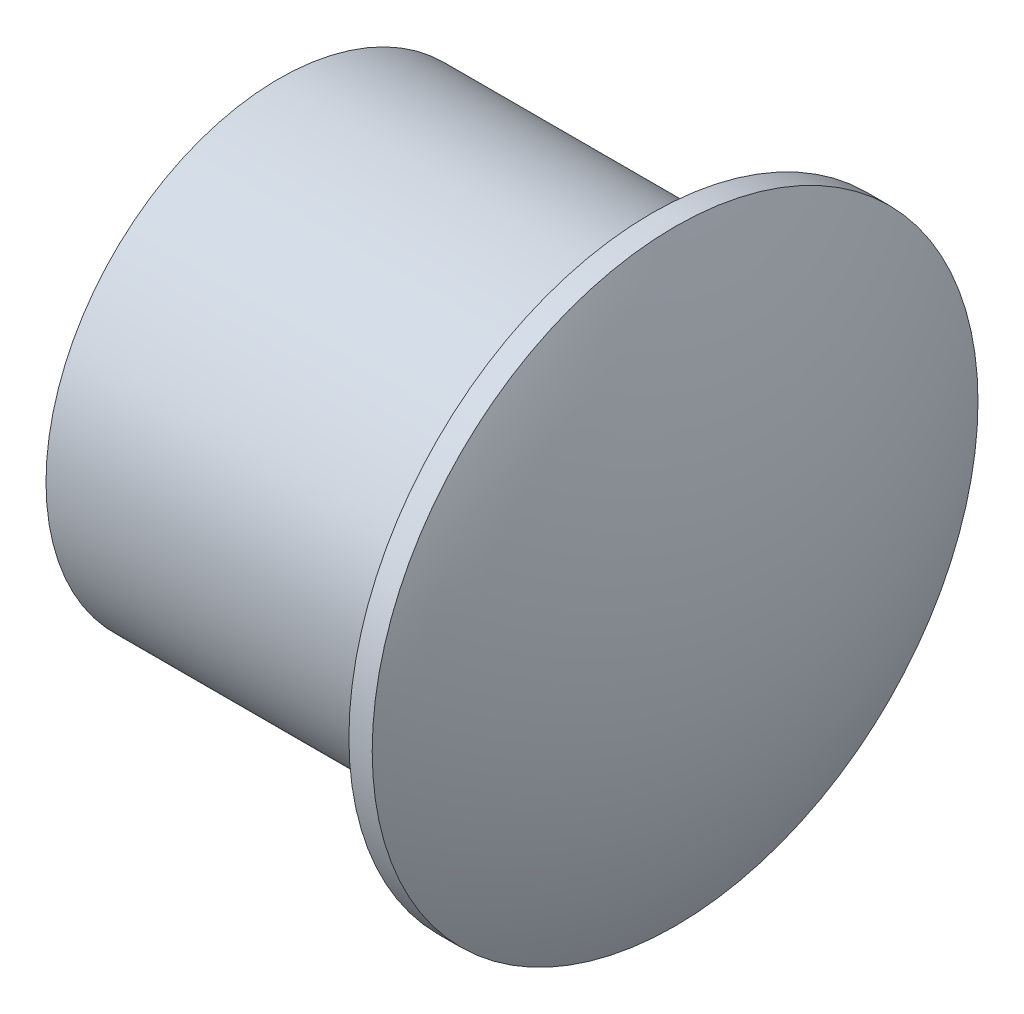
SolidWorks part; units mm, degrees
ref_plane "Front Plane" through (0, 0, 0) normal (0, 0, 1) x (1, 0, 0)
ref_plane "Top Plane" through (0, 0, 0) normal (0, 1, 0) x (1, 0, 0)
ref_plane "Right Plane" through (0, 0, 0) normal (1, 0, 0) x (0, 0, -1)
sketch "Sketch1" plane through (0, 0, 0) normal (0, 0, 1) x (1, 0, 0)
  line L0 (0, 0) -> (0, 10)
  line L1 (0, 10) -> (16, 10)
  line L2 (16, 10) -> (16, 13)
  line L3 (16, 13) -> (17, 13)
  line L4 (0, 0) -> (20, 0)
  arc A0 (20, 0) -> (17, 13) centre (-9.6667, 0) ccw
  dimension "D1" = 20
  dimension "D2" = 10
  dimension "D3" = 16
  dimension "D4" = 3
  dimension "D5" = 1
revolve "Revolve1" add sketch "Sketch1" angle 360 about L4
